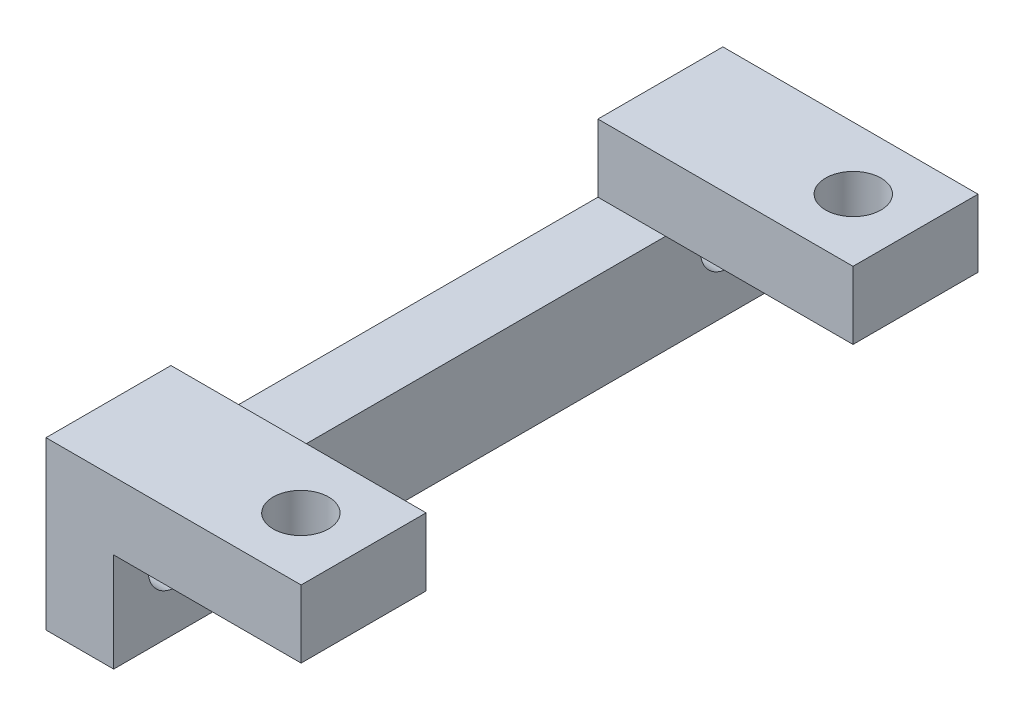
SolidWorks part; units mm, degrees
ref_plane "Front Plane" through (0, 0, 0) normal (0, 0, 1) x (1, 0, 0)
ref_plane "Top Plane" through (0, 0, 0) normal (0, 1, 0) x (1, 0, 0)
ref_plane "Right Plane" through (0, 0, 0) normal (1, 0, 0) x (0, 0, -1)
sketch "Sketch1" plane through (0, 0, 0) normal (1, 0, 0) x (0, 0, -1)
  line L1 (0, 0) -> (33.02, 0)
  line L2 (0, 0) -> (0, 4.826)
  line L3 (0, 4.826) -> (33.02, 4.826)
  line L4 (33.02, 0) -> (33.02, 4.826)
  dimension "D1" = 33.02
  dimension "D2" = 4.826
extrude "Boss-Extrude1" add sketch "Sketch1" along normal blind 3.302
sketch "Sketch2" plane through (0, 0, 0) normal (-1, 0, 0) x (0, 0, 1)
  line L0 (-33.02, 0) -> (-33.02, 4.826) construction
  line L1 (-33.02, 4.826) -> (-26.924, 4.826)
  line L2 (-33.02, 4.826) -> (-33.02, 8.128)
  line L3 (-33.02, 8.128) -> (-26.924, 8.128)
  line L4 (-26.924, 4.826) -> (-26.924, 8.128)
  line L5 (-33.02, 4.826) -> (0, 4.826) construction
  line L7 (0, 4.826) -> (-6.096, 4.826)
  line L8 (0, 4.826) -> (0, 8.128)
  line L9 (0, 8.128) -> (-6.096, 8.128)
  line L10 (-6.096, 4.826) -> (-6.096, 8.128)
  dimension "D1" = 6.096
  dimension "D2" = 3.302
extrude "Boss-Extrude2" add sketch "Sketch2" against normal blind 12.446
sketch "Sketch3" plane through (3.302, 0, 0) normal (1, 0, 0) x (0, 0, -1)
  line L0 (0, 0) -> (33.02, 0) construction
  line L1 (29.9847, 3.302) -> (3.0353, 3.302) construction
  point P0 (16.51, 0)
  point P1 (0, 0)
  point P6 (16.51, 3.302)
  dimension "D1" = 26.9494
  dimension "D2" = 3.302
hole_wizard "#6-32 Tapped Hole1" positions "Sketch4" profile "Sketch5" tap size "#6-32" standard "ANSI Inch" end condition through all
sketch "Sketch4" plane through (3.302, 0, 0) normal (1, 0, 0) x (0, 0, -1)
  point P0 (3.0353, 3.302)
  point P3 (29.9847, 3.302)
sketch "Sketch5" plane through (3.302, 3.302, -3.0353) normal (0, 1, 0) x (0, 0, -1)
  line L0 (0, 0) -> (0, 3.302)
  line L1 (0, 3.302) -> (1.3525, 3.302)
  line L2 (1.3525, 3.302) -> (1.3525, 0)
  line L5 (1.3525, 0) -> (0, 0)
  line L11 (0, -6.35) -> (0, 107.95) construction
  dimension "Thru Tap Drill Dia." = 2.7051
  dimension "Thru Tap Drill Depth" = 3.302
cosmetic thread "Hole Thread1" parameters "D2"=3.5052
cosmetic thread "Hole Thread2" parameters "D2"=3.5052
sketch "Sketch6" plane through (0, 8.128, 0) normal (0, 1, 0) x (1, 0, 0)
  line L0 (9.398, 3.0353) -> (9.398, 29.9847) construction
  line L1 (0, 0) -> (0, 6.096) construction
  point P0 (0, 0)
  point P3 (9.398, 16.51)
  dimension "D1" = 26.9494
  dimension "D2" = 9.398
hole_wizard "#6-32 Tapped Hole2" positions "Sketch7" profile "Sketch8" tap size "#6-32" standard "ANSI Inch" end condition through all
sketch "Sketch7" plane through (0, 8.128, 0) normal (0, 1, 0) x (1, 0, 0)
  point P0 (9.398, 3.0353)
  point P3 (9.398, 29.9847)
sketch "Sketch8" plane through (9.398, 8.128, -3.0353) normal (1, 0, 0) x (0, 0, 1)
  line L0 (0, 0) -> (0, 8.128)
  line L1 (0, 8.128) -> (1.3525, 8.128)
  line L2 (1.3525, 8.128) -> (1.3525, 0)
  line L5 (1.3525, 0) -> (0, 0)
  line L11 (0, -6.35) -> (0, 107.95) construction
  dimension "Thru Tap Drill Dia." = 2.7051
  dimension "Thru Tap Drill Depth" = 8.128
cosmetic thread "Hole Thread3" parameters "D2"=3.5052
cosmetic thread "Hole Thread4" parameters "D2"=3.5052
